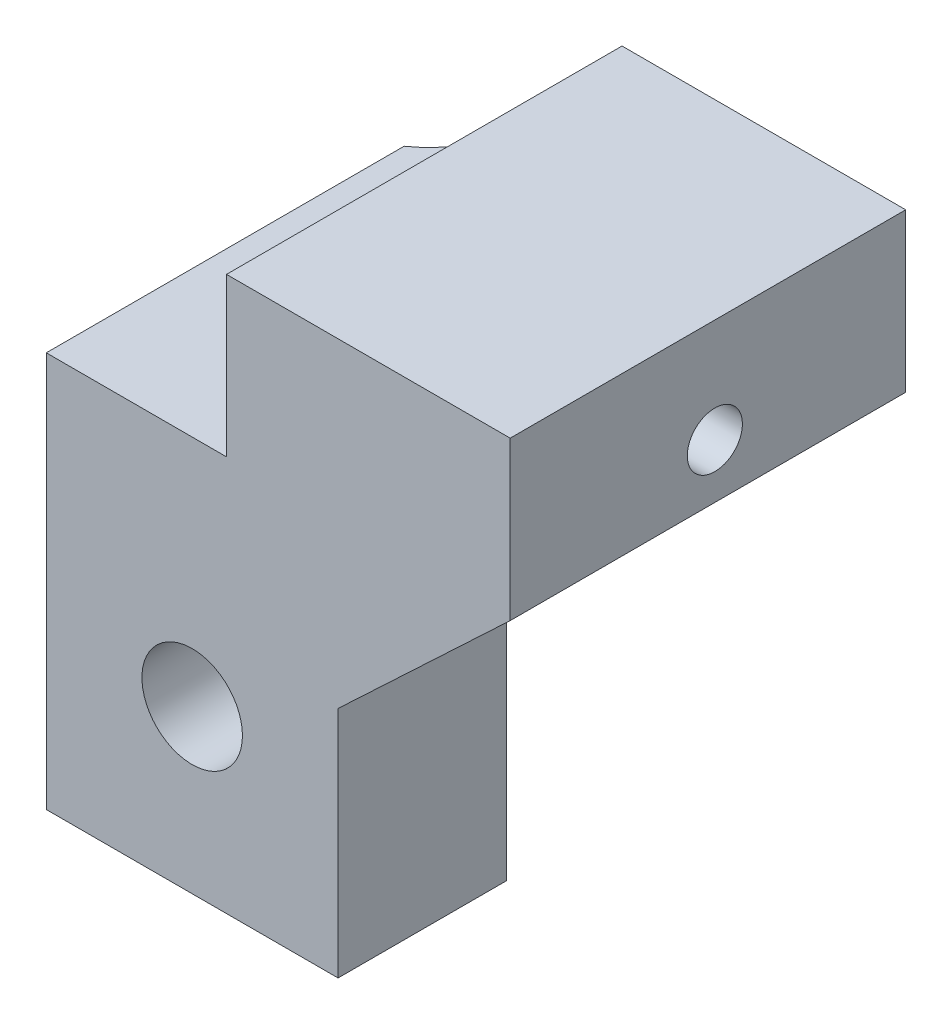
SolidWorks part; units mm, degrees
ref_plane "Front Plane" through (0, 0, 0) normal (0, 0, 1) x (1, 0, 0)
ref_plane "Top Plane" through (0, 0, 0) normal (0, 1, 0) x (1, 0, 0)
ref_plane "Right Plane" through (0, 0, 0) normal (1, 0, 0) x (0, 0, -1)
sketch "Sketch2" plane through (0, 0, -44.9704) normal (0, 0, 1) x (1, 0, 0)
  line L0 (-11.213, 58.3214) -> (-11.213, 70.5218)
  line L2 (-11.213, 70.5218) -> (-5.654, 70.5218)
  line L3 (-5.654, 70.5218) -> (-5.654, 75.3968)
  line L4 (-5.654, 75.3968) -> (-2.213, 75.3968)
  line L5 (-2.213, 75.3968) -> (-2.213, 58.3214)
  line L6 (-2.213, 58.3214) -> (-11.213, 58.3214)
  line L8 (-1.713, 61.9214) -> (-1.713, 63.3714) construction
  line L12 (-2.213, 75.3968) -> (3.096, 75.3968)
  line L13 (3.096, 75.3968) -> (3.096, 70.5218)
  line L14 (3.096, 70.5218) -> (-2.213, 65.5218)
  line L15 (-44.4509, 58.3214) -> (-40.568, 58.3214) construction
  line M15 (-6.243, 71.2218) -> (-6.243, 76.0968)
  dimension "D1" = 9
  dimension "D2" = 0.5
  dimension "D5" = 8.75
  dimension "D6" = 5
extrude "Boss-Extrude1" add sketch "Sketch2" against normal up to surface (12.2 mm away) contours L6 L5 L4 L3 L2 L0 M15 | L14 L13 L12 L5
sketch "Sketch3" plane through (-5.654, 0, 0) normal (-1, 0, 0) x (0, 0, 1)
  circle A0 centre (-51.2829, 72.1959) radius 0.85
  circle A1 centre (-51.0704, 100.8468) radius 0.85 construction
  point P5 (-51.2829, 72.1959)
extrude "Cut-Extrude1" cut sketch "Sketch3" against normal up to surface (8.75 mm away) up to face at (3.096, 72.9593, -51.0704)
sketch "Sketch4" plane through (0, 0, -44.9704) normal (0, 0, 1) x (1, 0, 0)
  line L0 (-6.713, 58.3214) -> (-6.713, 63.3214) construction
  line L1 (-2.213, 58.3214) -> (-11.213, 58.3214) construction
  line L3 (-2.213, 65.5218) -> (-2.213, 58.3214) construction
  line L5 (-6.713, 60.0305) -> (-3.863, 61.6759)
  line L6 (-3.863, 61.6759) -> (-3.863, 64.9668)
  line L7 (-3.863, 64.9668) -> (-6.713, 66.6123)
  line L8 (-6.713, 66.6123) -> (-9.563, 64.9668)
  line L9 (-9.563, 64.9668) -> (-9.563, 61.6759)
  line L10 (-9.563, 61.6759) -> (-6.713, 60.0305)
  circle A0 centre (-6.713, 63.3214) radius 1.55
  circle A1 centre (-6.713, 63.3214) radius 2.85 construction
  dimension "D1" = 3.1
  dimension "D2" = 5.7
  dimension "D3" = 5
extrude "Cut-Extrude2" cut sketch "Sketch4" against normal up to next contours A0
sketch "Sketch5" plane through (0, 0, -57.1704) normal (0, 0, -1) x (-1, 0, 0)
  line L0 (1.0551, 66.6123) -> (11.213, 66.6123)
  line L2 (2.213, 58.3214) -> (11.213, 58.3214) construction
  line L3 (-3.096, 70.5218) -> (2.213, 65.5218) construction
  line L4 (11.213, 58.3214) -> (11.213, 70.5218) construction
  circle M1 centre (6.713, 63.3214) radius 1.55
  line M2 (2.213, 65.5218) -> (2.213, 58.3214)
  line M3 (2.213, 58.3214) -> (11.213, 58.3214)
  line M4 (11.213, 58.3214) -> (11.213, 70.5218)
extrude "Cut-Extrude3" cut sketch "Sketch5" against normal blind 7 and the other way through all contours L0 M2 M3 M4 M1
ref_plane "Plane1" through (0, 0, -58.6829) normal (0, 0, -1) x (-1, 0, 0)
sketch "Sketch7" plane through (0, 0, -58.6829) normal (0, 0, -1) x (-1, 0, 0)
  line L4 (10.643, 74.9164) -> (9.4759, 66.6123) construction
  line L5 (10.643, 74.9164) -> (9.4759, 66.6123) construction
  line L6 (9.8234, 70.5218) -> (9.274, 66.6123)
  line L8 (11.213, 70.5218) -> (5.654, 70.5218) construction
  line L9 (9.274, 66.6123) -> (11.213, 66.6123)
  line L10 (11.213, 58.3214) -> (11.213, 70.5218) construction
  line L11 (11.213, 66.6123) -> (11.213, 70.5218)
  line L12 (11.213, 70.5218) -> (9.8234, 70.5218)
  line L13 (13.093, 78.2167) -> (13.093, 76.2276) construction
  line L14 (13.093, 74.9164) -> (13.093, 70.5164) construction
  dimension "D1" = 0.2
revolve "Cut-Revolve1" cut sketch "Sketch7" angle 360 about L13
